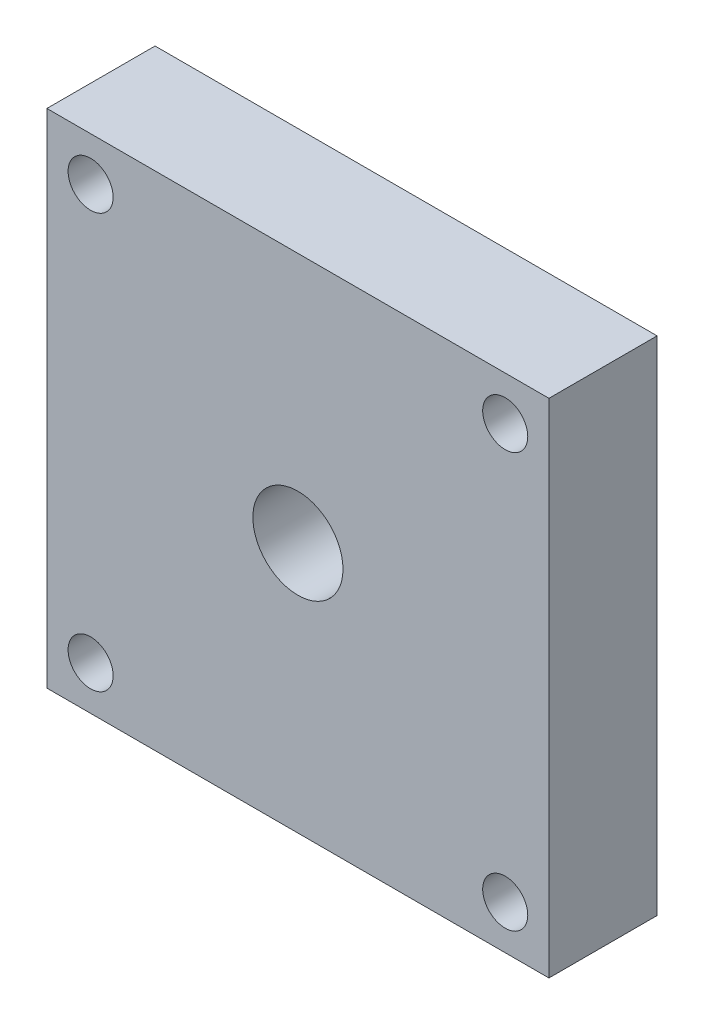
SolidWorks part; units mm, degrees
ref_plane "Plan de face" through (0, 0, 0) normal (0, 0, 1) x (1, 0, 0)
ref_plane "Plan de dessus" through (0, 0, 0) normal (0, 1, 0) x (1, 0, 0)
ref_plane "Plan de droite" through (0, 0, 0) normal (1, 0, 0) x (0, 0, -1)
sketch "Esquisse1" plane through (0, 0, 0) normal (0, 0, 1) x (1, 0, 0)
  line L1 (-12.8893, 11.6233) -> (14.9607, 11.6233)
  line L2 (-12.8893, 11.6233) -> (-12.8893, -16.2267)
  line L3 (-12.8893, -16.2267) -> (14.9607, -16.2267)
  line L4 (14.9607, 11.6233) -> (14.9607, -16.2267)
  circle A0 centre (12.5357, 9.1933) radius 1.25
  circle A1 centre (-10.4643, 9.1933) radius 1.25
  circle A2 centre (-10.4643, -13.7967) radius 1.25
  circle A3 centre (12.5357, -13.7967) radius 1.25
  circle A4 centre (1.0357, -2.3017) radius 2.5
  dimension "D3" = 23
  dimension "D4" = 2.43
  dimension "D5" = 2.5
  dimension "D6" = 2.43
  dimension "D7" = 23
  dimension "D8" = 2.5
  dimension "D9" = 2.5
  dimension "D10" = 2.43
  dimension "D11" = 11.5
  dimension "D12" = 11.5
  dimension "D13" = 2.43
  dimension "D14" = 2.5
  dimension "D15" = 5
  dimension "D16" = 13.925
  dimension "D17" = 13.925
  dimension "D1" = 27.85
  dimension "D2" = 27.85
extrude "Boss.-Extru.1" add sketch "Esquisse1" along normal blind 6
